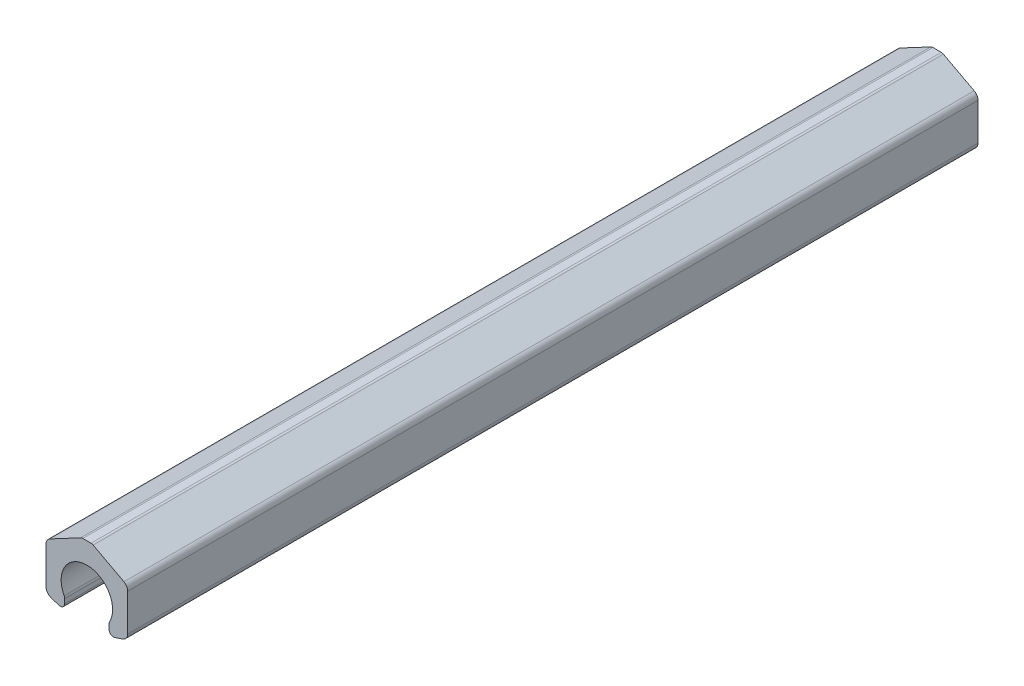
SolidWorks part; units mm, degrees
material "6061 Alloy"
ref_plane "Front Plane" through (0, 0, 0) normal (0, 0, 1) x (1, 0, 0)
ref_plane "Top Plane" through (0, 0, 0) normal (0, 1, 0) x (1, 0, 0)
ref_plane "Right Plane" through (0, 0, 0) normal (1, 0, 0) x (0, 0, -1)
sketch "Sketch1" plane through (0, 0, 0) normal (0, 0, 1) x (1, 0, 0)
  line L0 (2.9718, 33.528) -> (-2.9718, 33.528)
  line L1 (-4.4611, 33.1571) -> (-26.5613, 21.4194)
  line L2 (-29.2989, 16.8656) -> (-29.2989, -9.652)
  line L3 (-15.875, -13.4506) -> (-15.875, -10.2407)
  line L4 (15.875, -10.2407) -> (15.875, -13.4506)
  line L5 (29.2989, -9.652) -> (29.2989, 16.8656)
  line L6 (26.5613, 21.4194) -> (4.4611, 33.1571)
  line L7 (0, 0) -> (0, 31.9929) construction
  arc A0 (4.4611, 33.1571) -> (2.9718, 33.528) centre (2.9718, 30.353) ccw
  arc A1 (-2.9718, 33.528) -> (-4.4611, 33.1571) centre (-2.9718, 30.353) ccw
  arc A2 (-26.5613, 21.4194) -> (-29.2989, 16.8656) centre (-24.1427, 16.8656) ccw
  arc A3 (-29.2989, -9.652) -> (-25.9998, -14.4621) centre (-24.1427, -9.652) ccw
  arc A4 (-25.9998, -14.4621) -> (-19.9264, -16.5022) centre (0, 52.8798) ccw
  arc A5 (-19.9264, -16.5022) -> (-15.875, -13.4506) centre (-19.05, -13.4506) ccw
  arc A6 (-15.875, -10.2407) -> (-16.2535, -8.7374) centre (-19.05, -10.2407) ccw
  arc A7 (-16.2535, -8.7374) -> (16.2535, -8.7374) centre (0, 0) cw
  arc A8 (16.2535, -8.7374) -> (15.875, -10.2407) centre (19.05, -10.2407) ccw
  arc A9 (15.875, -13.4506) -> (19.9264, -16.5022) centre (19.05, -13.4506) ccw
  arc A10 (19.9264, -16.5022) -> (25.9998, -14.4621) centre (0, 52.8798) ccw
  arc A11 (25.9998, -14.4621) -> (29.2989, -9.652) centre (24.1427, -9.652) ccw
  arc A12 (29.2989, 16.8656) -> (26.5613, 21.4194) centre (24.1427, 16.8656) ccw
  dimension "D1" = 36.9062
  dimension "D3" = 3.175
  dimension "D5" = 5.1562
  dimension "D10" = 72.1868
  dimension "D11" = 3.175
  dimension "D12" = 15.875
  dimension "D2" = 5.9436
  dimension "D4" = 33.528
  dimension "D6" = 29.2989
  dimension "D7" = 58.5978
  dimension "D8" = 26.5176
  dimension "D9" = 9.652
  dimension "D13" = 31.75
extrude "Extrude1" add sketch "Sketch1" against normal blind 609.6
